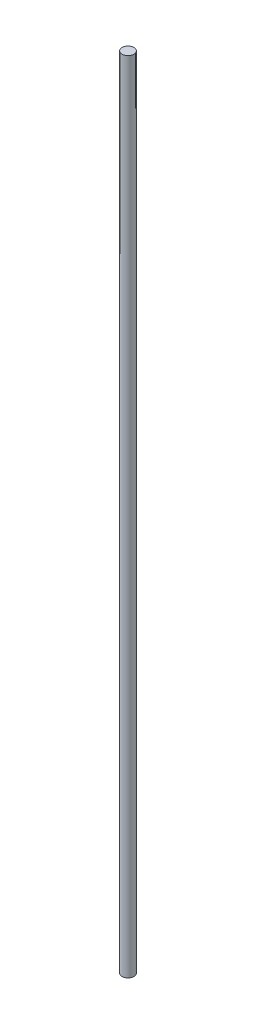
SolidWorks part; units mm, degrees
ref_plane "Alzado" through (0, 0, 0) normal (0, 0, 1) x (1, 0, 0)
ref_plane "Planta" through (0, 0, 0) normal (0, 1, 0) x (1, 0, 0)
ref_plane "Vista lateral" through (0, 0, 0) normal (1, 0, 0) x (0, 0, -1)
sketch "Croquis1" plane through (0, 0, 0) normal (0, 1, 0) x (1, 0, 0)
  circle A0 centre (0, 0) radius 6.35
  dimension "D1" = 12.7
sketch "Croquis2" plane through (0, 0, 0) normal (0, 0, 1) x (1, 0, 0)
  line L0 (0, 0) -> (0, 860)
  dimension "D1" = 860
sweep "Barrer1" add profiles "Croquis1" path "Croquis2"
